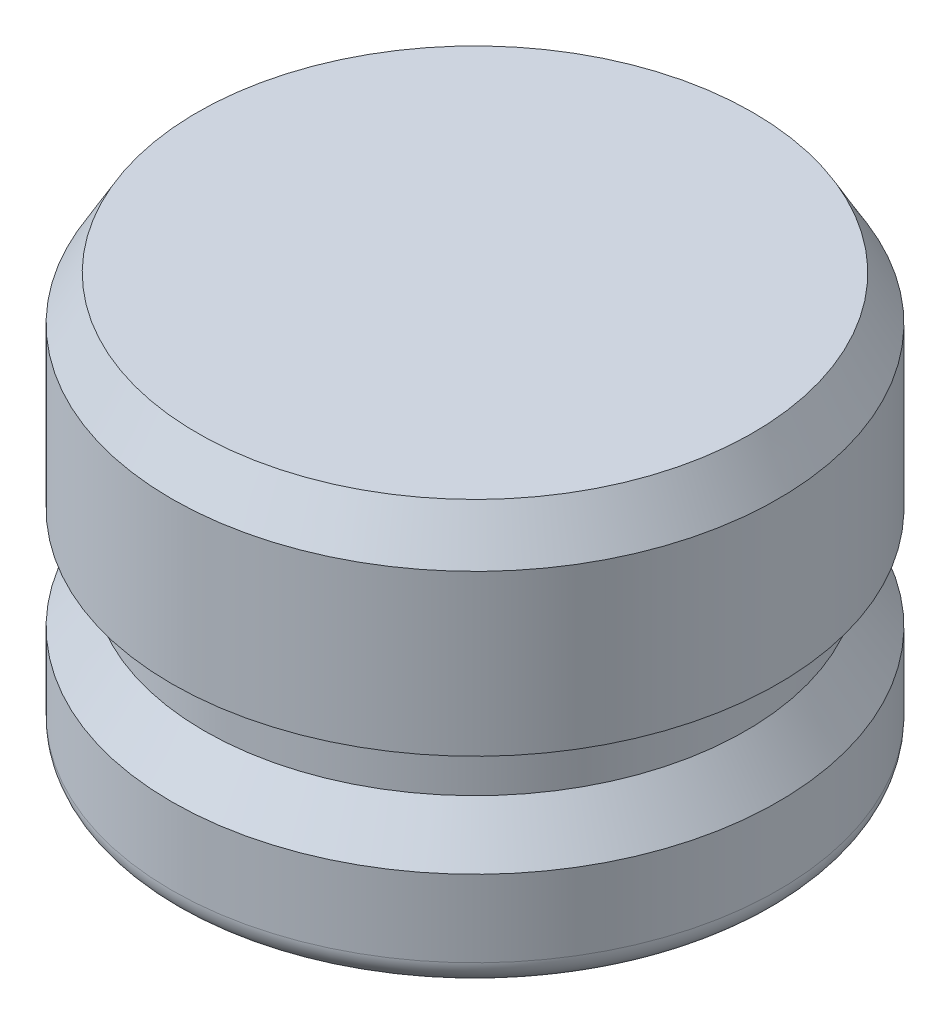
SolidWorks part; units mm, degrees
ref_plane "Front Plane" through (0, 0, 0) normal (0, 0, 1) x (1, 0, 0)
ref_plane "Top Plane" through (0, 0, 0) normal (0, 1, 0) x (1, 0, 0)
ref_plane "Right Plane" through (0, 0, 0) normal (1, 0, 0) x (0, 0, -1)
sketch "Sketch1" plane through (0, 0, 0) normal (0, 0, 1) x (1, 0, 0)
  line L0 (0, 0) -> (0, 12.7) construction
  line L1 (0, 0) -> (-9.4234, 0)
  line L2 (-9.4234, 0) -> (-9.4234, 3.175)
  line L4 (-8.4074, 4.572) -> (-8.4074, 6.35)
  line L5 (-8.4074, 6.35) -> (-9.4234, 6.35)
  line L6 (-9.4234, 6.35) -> (-9.4234, 12.7)
  line L7 (-9.4234, 12.7) -> (0, 12.7)
  line L8 (-9.525, 16.6801) -> (-9.525, -9.6051) construction
  line L9 (0, 0) -> (0, 12.7)
  line L10 (-8.4074, 4.572) -> (-9.4234, 3.175)
  dimension "D1" = 12.7
  dimension "D2" = 9.4234
  dimension "D3" = 1.778
  dimension "D4" = 3.175
  dimension "D5" = 9.525
  dimension "D6" = 8.4074
  dimension "D7" = 6.35
revolve "Revolve1" add sketch "Sketch1" angle 360 about L9
fillet "Fillet1" radius 0.7937 1 edges at (0, 0, -9.4234)
chamfer "Chamfer1" distance 0.7937 angle 60 1 edges at (0, 12.7, -9.4234)
